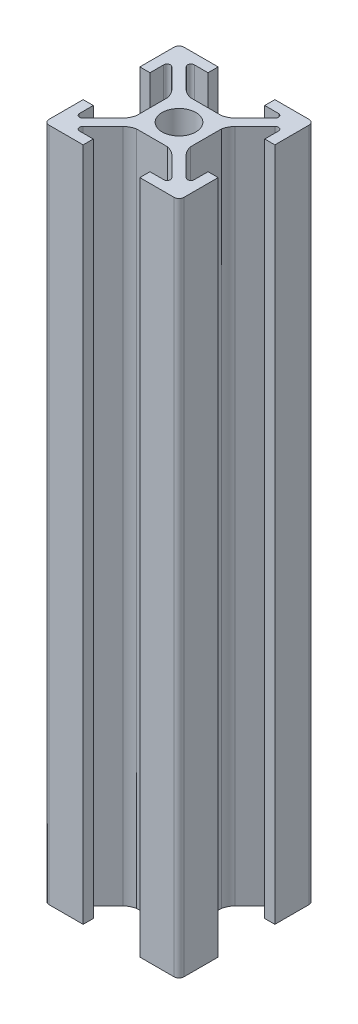
SolidWorks part; units mm, degrees
ref_plane "Front Plane" through (0, 0, 0) normal (0, 0, 1) x (1, 0, 0)
ref_plane "Top Plane" through (0, 0, 0) normal (0, 1, 0) x (1, 0, 0)
ref_plane "Right Plane" through (0, 0, 0) normal (1, 0, 0) x (0, 0, -1)
sketch "Sketch1" plane through (0, 0, 0) normal (0, 1, 0) x (1, 0, 0)
  line L0 (-3.611, 4.6716) -> (-6.5858, 7.6464)
  line L1 (9.25, -10) -> (4.2, -10)
  line L2 (10, -9.25) -> (10, -4.2)
  line L3 (9.25, 10) -> (4.2, 10)
  line L4 (-10, -9.25) -> (-10, -4.2)
  line L5 (10, -10) -> (-10, 10) construction
  line L6 (10, 10) -> (-10, -10) construction
  line L7 (2.2681, -4) -> (-2.2681, -4)
  line L8 (4, -2.2681) -> (4, 2.2681)
  line L9 (2.2681, 4) -> (-2.2681, 4)
  line L10 (-4, -2.2681) -> (-4, 2.2681)
  line L11 (4, -4) -> (-4, 4) construction
  line L12 (4, 4) -> (-4, -4) construction
  line L13 (-6.2322, 8.5) -> (-4.2, 8.5)
  line L14 (-4.2, 8.5) -> (-4.2, 10)
  line L15 (4.6716, 3.611) -> (7.6464, 6.5858)
  line L16 (8.5, 6.2322) -> (8.5, 4.2)
  line L17 (8.5, 4.2) -> (10, 4.2)
  line L18 (4.2, 8.5) -> (4.2, 10)
  line L19 (-8.5, 4.2) -> (-10, 4.2)
  line L20 (-8.5, 6.2322) -> (-8.5, 4.2)
  line L21 (-4.6716, 3.611) -> (-7.6464, 6.5858)
  line L22 (0, 10) -> (0, -10) construction
  line L23 (6.2322, 8.5) -> (4.2, 8.5)
  line L24 (3.611, 4.6716) -> (6.5858, 7.6464)
  line L25 (-55, 0) -> (55, 0) construction
  line L26 (3.611, -4.6716) -> (6.5858, -7.6464)
  line L27 (6.2322, -8.5) -> (4.2, -8.5)
  line L28 (-4.6716, -3.611) -> (-7.6464, -6.5858)
  line L29 (-8.5, -6.2322) -> (-8.5, -4.2)
  line L30 (-8.5, -4.2) -> (-10, -4.2)
  line L31 (4.2, -8.5) -> (4.2, -10)
  line L32 (8.5, -4.2) -> (10, -4.2)
  line L33 (8.5, -6.2322) -> (8.5, -4.2)
  line L34 (4.6716, -3.611) -> (7.6464, -6.5858)
  line L35 (-4.2, -8.5) -> (-4.2, -10)
  line L36 (-6.2322, -8.5) -> (-4.2, -8.5)
  line L37 (2.2681, -4) -> (-2.2681, -4)
  line L38 (10, -10) -> (4.2, -10)
  line L39 (-3.611, -4.6716) -> (-6.5858, -7.6464)
  line L40 (-4.2, 10) -> (-9.25, 10)
  line L41 (-10, 4.2) -> (-10, 9.25)
  line L42 (-4.2, -10) -> (-9.25, -10)
  line L43 (-4.2, -10) -> (-10, -10)
  line L44 (10, 4.2) -> (10, 9.25)
  circle A0 centre (0, 0) radius 2.5
  arc A1 (-8.5, 6.2322) -> (-7.6464, 6.5858) centre (-8, 6.2322) cw
  arc A2 (-6.5858, 7.6464) -> (-6.2322, 8.5) centre (-6.2322, 8) cw
  arc A3 (-3.611, 4.6716) -> (-2.2681, 4) centre (-1.7294, 6.7555) ccw
  arc A4 (-4.6716, 3.611) -> (-4, 2.2681) centre (-6.7555, 1.7294) cw
  arc A5 (4.6716, 3.611) -> (4, 2.2681) centre (6.7555, 1.7294) ccw
  arc A6 (3.611, 4.6716) -> (2.2681, 4) centre (1.7294, 6.7555) cw
  arc A7 (6.5858, 7.6464) -> (6.2322, 8.5) centre (6.2322, 8) ccw
  arc A8 (8.5, 6.2322) -> (7.6464, 6.5858) centre (8, 6.2322) ccw
  arc A9 (8.5, -6.2322) -> (7.6464, -6.5858) centre (8, -6.2322) cw
  arc A10 (6.5858, -7.6464) -> (6.2322, -8.5) centre (6.2322, -8) cw
  arc A11 (3.611, -4.6716) -> (2.2681, -4) centre (1.7294, -6.7555) ccw
  arc A12 (4.6716, -3.611) -> (4, -2.2681) centre (6.7555, -1.7294) cw
  arc A13 (-4.6716, -3.611) -> (-4, -2.2681) centre (-6.7555, -1.7294) ccw
  arc A14 (-3.611, -4.6716) -> (-2.2681, -4) centre (-1.7294, -6.7555) cw
  arc A15 (-6.5858, -7.6464) -> (-6.2322, -8.5) centre (-6.2322, -8) ccw
  arc A16 (-8.5, -6.2322) -> (-7.6464, -6.5858) centre (-8, -6.2322) ccw
  arc A17 (-9.25, -10) -> (-10, -9.25) centre (-9.25, -9.25) cw
  arc A18 (9.25, -10) -> (10, -9.25) centre (9.25, -9.25) ccw
  arc A19 (10, 9.25) -> (9.25, 10) centre (9.25, 9.25) ccw
  arc A20 (-9.25, 10) -> (-10, 9.25) centre (-9.25, 9.25) ccw
  point P0 (0, 0)
  point P18 (-8.5, 7.4393)
  point P24 (-7.4393, 8.5)
  point P50 (7.4393, 8.5)
  point P51 (8.5, 7.4393)
  point P86 (8.5, -7.4393)
  point P87 (7.4393, -8.5)
  point P88 (-7.4393, -8.5)
  point P89 (-8.5, -7.4393)
  dimension "D2" = 5
  dimension "D7" = 0.5
  dimension "D8" = 0.75
  dimension "D1" = 20
  dimension "D3" = 8
  dimension "D4" = 1.5
  dimension "D5" = 1.5
  dimension "D6" = 8.4
extrude "Boss-Extrude1" add sketch "Sketch1" along normal blind 100 contours L40 A20 L41 L19 L20 A1 L21 A4 L10 A13 L28 A16 L29 L30 L4 A17 L42 L35 L36 A15 L39 A14 L7 A11 L26 A10 L27 L31 L1 A18 L2 L32 L33 A9 L34 A12 L8 A5 L15 A8 L16 L17 L44 A19 L3 L18 L23 A7 L24 A6 L9
